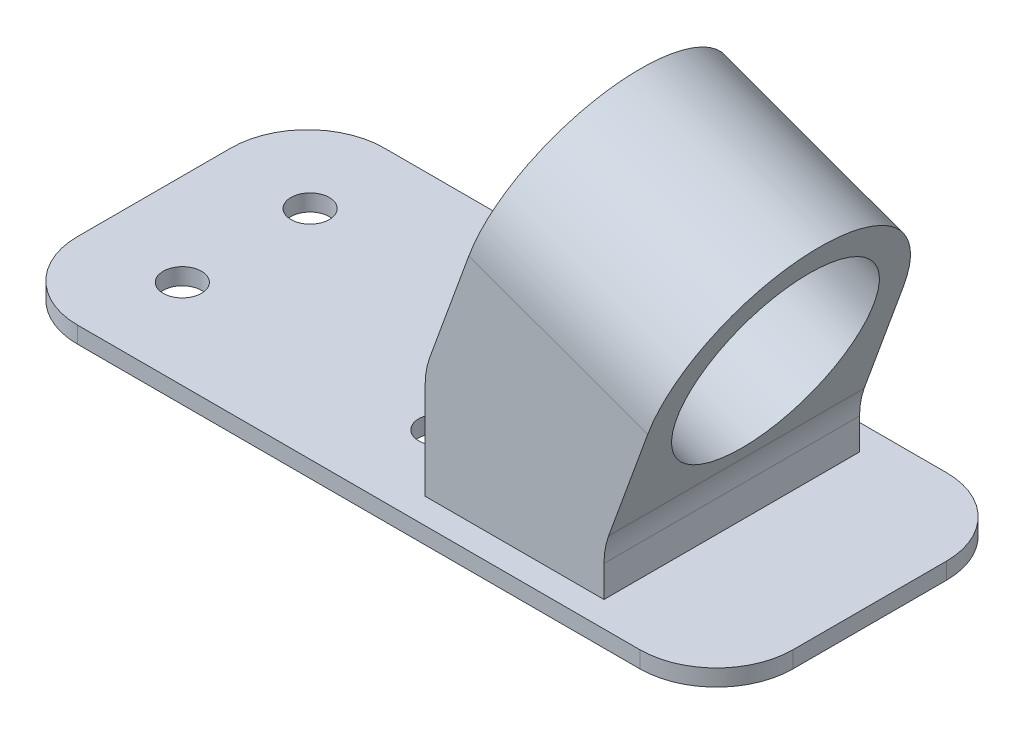
SolidWorks part; units mm, degrees
ref_plane "Front Plane" through (0, 0, 0) normal (0, 0, 1) x (1, 0, 0)
ref_plane "Top Plane" through (0, 0, 0) normal (0, 1, 0) x (1, 0, 0)
ref_plane "Right Plane" through (0, 0, 0) normal (1, 0, 0) x (0, 0, -1)
sketch "Sketch1" plane through (0, 0, 0) normal (0, 1, 0) x (1, 0, 0)
  line L1 (-11, -6) -> (11, -6)
  line L2 (-14, -3) -> (-14, 3)
  line L3 (-11, 6) -> (11, 6)
  line L4 (14, -3) -> (14, 3)
  line L5 (-14, -6) -> (14, 6) construction
  line L6 (-14, 6) -> (14, -6) construction
  arc A0 (11, 6) -> (14, 3) centre (11, 3) cw
  arc A1 (14, -3) -> (11, -6) centre (11, -3) cw
  arc A2 (-11, -6) -> (-14, -3) centre (-11, -3) cw
  arc A3 (-14, 3) -> (-11, 6) centre (-11, 3) cw
  point P0 (0, 0)
  dimension "D3" = 3
  dimension "D1" = 28
  dimension "D2" = 12
extrude "Boss-Extrude1" add sketch "Sketch1" along normal blind 0.65
sketch "Sketch2" plane through (0, 0.65, 0) normal (0, 1, 0) x (1, 0, 0)
  line L0 (-14, 0) -> (14, 0) construction
  line L1 (-14, 3) -> (-14, -3) construction
  line L2 (14, -3) -> (14, 3) construction
  line L4 (1.6, -5) -> (8.6, -5)
  line L5 (1.6, -5) -> (1.6, 5)
  line L6 (1.6, 5) -> (8.6, 5)
  line L7 (8.6, -5) -> (8.6, 5)
  line L8 (1.6, -5) -> (8.6, 5) construction
  line L9 (1.6, 5) -> (8.6, -5) construction
  point P6 (5.1, 0)
  point P11 (0, 0)
  point P12 (0, 0)
  point P13 (0, 0)
  dimension "D1" = 7
  dimension "D2" = 10
  dimension "D3" = 5.4
sketch "Sketch6" plane through (0, 0.65, 0) normal (0, 1, 0) x (1, 0, 0)
  line L0 (-14, 0) -> (14, 0) construction
  line L1 (-10.4, -2.5) -> (-0.4, -2.5) construction
  line L2 (-10.4, -2.5) -> (-10.4, 2.5) construction
  line L3 (-10.4, 2.5) -> (-0.4, 2.5) construction
  line L4 (-0.4, -2.5) -> (-0.4, 2.5) construction
  line L5 (-10.4, -2.5) -> (-0.4, 2.5) construction
  line L6 (-10.4, 2.5) -> (-0.4, -2.5) construction
  line L7 (1.6, -5) -> (1.6, 5) construction
  circle A0 centre (-10.4, 2.5) radius 0.75
  circle A1 centre (-0.4, 2.5) radius 0.75
  circle A2 centre (-0.4, -2.5) radius 0.75
  circle A3 centre (-10.4, -2.5) radius 0.75
  point P0 (-5.4, 0)
  point P12 (-0.4, 0)
  dimension "D3" = 1.5
  dimension "D1" = 2
  dimension "D2" = 10
  dimension "D4" = 5
sketch "Sketch7" plane through (0, 0, 0) normal (0, 0, 1) x (1, 0, 0)
  line L0 (14, 0) -> (-14, 0) construction
  line L1 (14, 0) -> (-12.3114, -9.5766) construction
  line L2 (0, 0) -> (1.6377, -4.4995)
  dimension "D1" = 20
ref_plane "Plane1" through (0, 0, 5) normal (0, 0, 1) x (1, 0, 0)
sketch "Sketch8" plane through (0, 0, 5) normal (0, 0, 1) x (1, 0, 0)
  line L0 (1.6, 0.65) -> (1.6, 4.9478)
  line L1 (1.6, 0.65) -> (8.6, 0.65) construction
  line L2 (1.6, 0.65) -> (8.6, 0.65) construction
  line L4 (1.6, 0.65) -> (8.6, 0.65) construction
  line L5 (8.6, 0.65) -> (1.6, 0.65)
  line L7 (1.6, 4.9478) -> (8.6, 2.4)
  line L8 (8.6, 2.4) -> (8.6, 0.65)
  point P11 (1.6, 0.65)
  point P12 (8.6, 0.65)
  dimension "D1" = 20
  dimension "D2" = 1.75
extrude "Boss-Extrude2" add sketch "Sketch8" against normal up to vertex (10 mm away) up to point (8.6, 0.65, -5)
sketch "Sketch9" plane through (1.7774, 4.8832, 0) normal (0.342, 0.9397, 0) x (0.9397, -0.342, 0)
  line L0 (7.2605, 5) -> (7.2605, -5) construction
  line L1 (-0.1887, 5) -> (7.2605, 5)
  line L2 (-0.1887, 5) -> (-0.1887, -5)
  line L3 (-0.1887, -5) -> (7.2605, -5)
  line L4 (7.2605, 5) -> (7.2605, -5)
extrude "Boss-Extrude3" add sketch "Sketch9" along normal blind 10
sketch "Sketch10" plane through (-0.1774, 0.0646, 0) normal (-0.9397, 0.342, 0) x (0, 0, 1)
  line L0 (-5, 15.1966) -> (-5, 5.1966) construction
  line L1 (-5, 15.1966) -> (5, 15.1966) construction
  line L2 (-5, 10.1966) -> (-5, 15.1966)
  line L3 (-5, 15.1966) -> (5, 15.1966)
  line L4 (5, 15.1966) -> (5, 10.1966)
  arc A0 (-5, 10.1966) -> (5, 10.1966) centre (0, 10.1966) cw
  circle A1 centre (0, 10.1966) radius 3.85
  line M6 (5, 5.1966) -> (5, 15.1966)
  line M7 (5, 15.1966) -> (-5, 15.1966)
  line M8 (-5, 15.1966) -> (-5, 5.1966)
  dimension "D1" = 5
  dimension "D2" = 7.7
extrude "Cut-Extrude1" cut sketch "Sketch10" against normal up to next contours A0 M7 M6 | A0 L3 M8 | A1
extrude "Cut-Extrude2" cut sketch "Sketch6" against normal up to next
fillet "Fillet1" radius 3 2 edges at (1.6, 4.9478, 0) (8.6, 2.4, 0)
